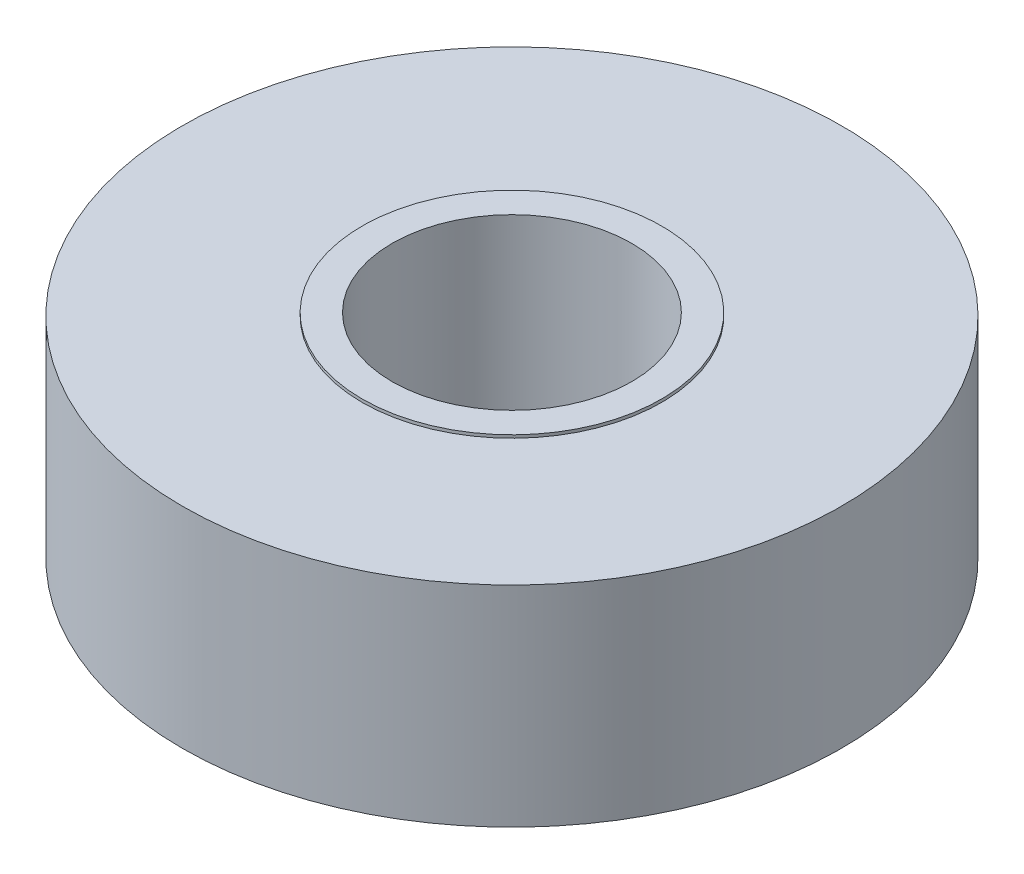
SolidWorks part; units mm, degrees
ref_plane "Alzado" through (0, 0, 0) normal (0, 0, 1) x (1, 0, 0)
ref_plane "Planta" through (0, 0, 0) normal (0, 1, 0) x (1, 0, 0)
ref_plane "Vista lateral" through (0, 0, 0) normal (1, 0, 0) x (0, 0, -1)
sketch "Croquis1" plane through (0, 0, 0) normal (0, 1, 0) x (1, 0, 0)
  circle A0 centre (0, 0) radius 4
  circle A1 centre (0, 0) radius 11
  dimension "D1" = 22
  dimension "D2" = 8
extrude "Saliente-Extruir1" add sketch "Croquis1" along normal mid plane 7
sketch "Croquis2" plane through (0, 0, 0) normal (0, 1, 0) x (1, 0, 0)
  circle A0 centre (0, 0) radius 5
  circle A1 centre (0, 0) radius 4
  dimension "D1" = 10
  dimension "D2" = 8
extrude "Saliente-Extruir2" add sketch "Croquis2" along normal mid plane 7.2
